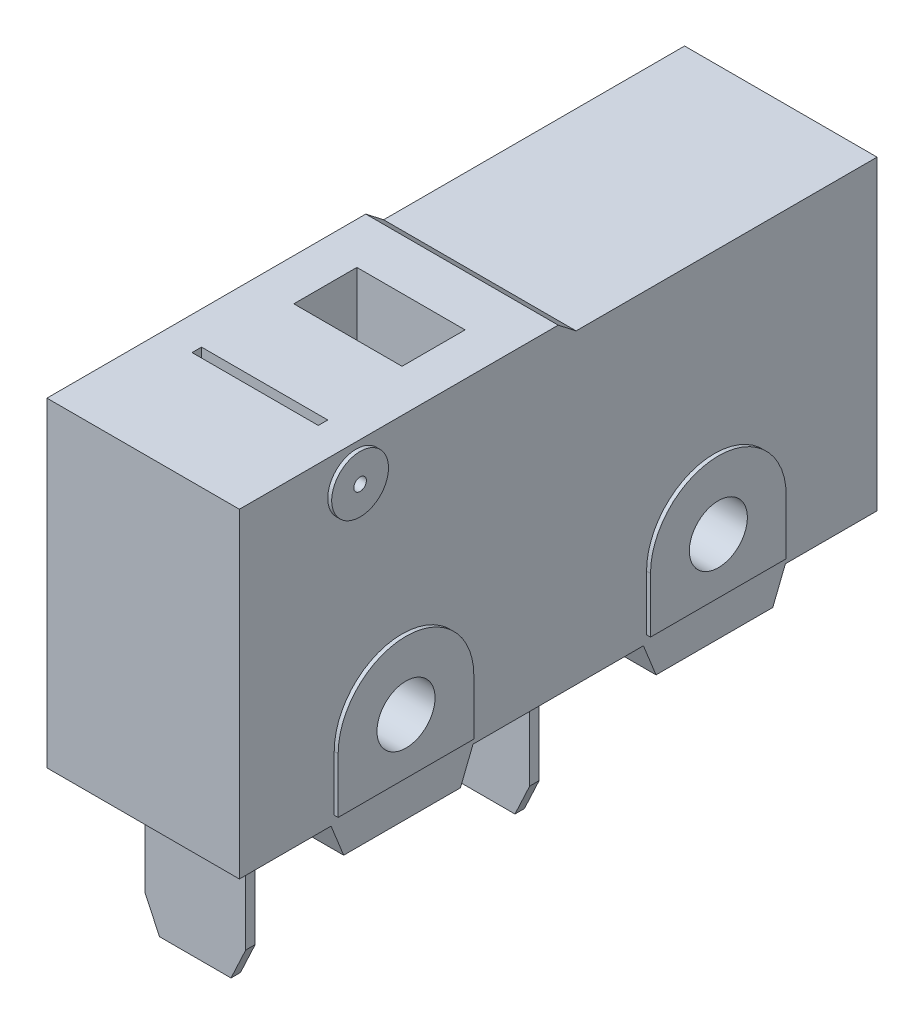
SolidWorks part; units mm, degrees
ref_plane "Front Plane" through (0, 0, 0) normal (0, 0, 1) x (1, 0, 0)
ref_plane "Top Plane" through (0, 0, 0) normal (0, 1, 0) x (1, 0, 0)
ref_plane "Right Plane" through (0, 0, 0) normal (1, 0, 0) x (0, 0, -1)
sketch "Sketch1" plane through (0, 0, 0) normal (1, 0, 0) x (0, 0, -1)
  line L1 (-10.105, 4.855) -> (10.105, 4.855)
  line L2 (-10.105, 4.855) -> (-10.105, -4.855)
  line L3 (-10.105, -4.855) -> (10.105, -4.855)
  line L4 (10.105, 4.855) -> (10.105, -4.855)
  line L5 (-10.105, 4.855) -> (10.105, -4.855) construction
  line L6 (-10.105, -4.855) -> (10.105, 4.855) construction
  point P0 (0, 0)
  point P6 (-10.105, 0)
  dimension "D1" = 20.21
  dimension "D2" = 9.71
extrude "Boss-Extrude1" add sketch "Sketch1" along normal mid plane 6.1
sketch "Sketch4" plane through (0, 0, 0) normal (1, 0, 0) x (0, 0, -1)
  line L0 (-7.2, -4.855) -> (-6.8, -5.855)
  line L1 (-7.2, -2.7338) -> (-7.2, -5.855) construction
  line L2 (-10.105, -4.855) -> (10.105, -4.855) construction
  line L3 (-7.2, -5.855) -> (-2.7, -5.855) construction
  line L4 (-6.8, -5.855) -> (-3.1, -5.855)
  line L5 (-3.1, -5.855) -> (-2.7, -4.855)
  line L6 (-2.7, -5.855) -> (-2.7, -2.7338) construction
  line L7 (-2.7, -4.855) -> (-7.2, -4.855)
  line L8 (-4.95, 0.2162) -> (-4.95, -6.3046) construction
  line L9 (0, 6.1609) -> (0, -8.528) construction
  line L10 (2.7, -4.855) -> (7.2, -4.855)
  line L11 (3.1, -5.855) -> (2.7, -4.855)
  line L12 (6.8, -5.855) -> (3.1, -5.855)
  line L13 (7.2, -4.855) -> (6.8, -5.855)
  line L14 (-10.105, 4.855) -> (-10.105, 5.295)
  line L15 (-10.105, 5.295) -> (0, 5.295)
  line L16 (0, 5.295) -> (0.5663, 4.855)
  line L17 (10.105, 4.855) -> (-10.105, 4.855) construction
  line L18 (-10.105, 4.855) -> (0.5663, 4.855)
  point P8 (-4.95, -5.855)
  dimension "D1" = 3.7
  dimension "D2" = 10.15
sketch "Mounting Holes" plane through (0, 0, 0) normal (1, 0, 0) x (0, 0, -1)
  line L0 (-10.105, -4.855) -> (10.105, -4.855) construction
  line L1 (-4.95, -2.855) -> (4.95, -2.855) construction
  circle A0 centre (-4.95, -2.855) radius 0.92
  circle A1 centre (4.95, -2.855) radius 0.92
  point P7 (0, -2.855)
  dimension "D1" = 1.84
  dimension "D2" = 2
  dimension "D3" = 9.9
sketch "Sketch3" plane through (0, 0, 0) normal (1, 0, 0) x (0, 0, -1)
  line L4 (-6.8691, -0.455) -> (-3.0762, -0.455) construction
  line L6 (-4.95, 0.2162) -> (-4.95, -6.3046) construction
  line L8 (-7.1, -2.855) -> (-7.1, -4.605)
  line L9 (-7.1, -4.605) -> (-2.8, -4.605)
  line L10 (-2.8, -4.605) -> (-2.8, -2.855)
  line L11 (-10.105, -4.855) -> (10.105, -4.855) construction
  line L12 (0, 1.4439) -> (0, -5.6534) construction
  line L13 (4.95, 0.2162) -> (4.95, -6.3046) construction
  line L14 (6.8691, -0.455) -> (3.0762, -0.455) construction
  line L15 (2.8, -4.605) -> (2.8, -2.855)
  line L16 (7.1, -4.605) -> (2.8, -4.605)
  line L17 (7.1, -2.855) -> (7.1, -4.605)
  arc A0 (-2.8, -2.855) -> (-7.1, -2.855) centre (-4.95, -2.855) ccw
  arc A1 (2.8, -2.855) -> (7.1, -2.855) centre (4.95, -2.855) cw
  dimension "D1" = 4.3
  dimension "D2" = 0.25
extrude "Boss-Extrude2" add sketch "Sketch4" along normal mid plane 6.1
extrude "Boss-Extrude3" add sketch "Sketch3" along normal mid plane 6.35
extrude "Cut-Extrude1" cut sketch "Mounting Holes" against normal through all both and the other way through all
sketch "Sketch5" plane through (0, 0, 0) normal (1, 0, 0) x (0, 0, -1)
  line L0 (-10.105, 5.295) -> (-10.105, -4.855) construction
  line L1 (0, 5.295) -> (-10.105, 5.295) construction
  circle A0 centre (-6.405, 4.195) radius 0.9
  dimension "D1" = 1.8
  dimension "D2" = 3.7
  dimension "D3" = 1.1
extrude "Boss-Extrude4" add sketch "Sketch5" along normal mid plane 6.35
sketch "Sketch6" plane through (0, 0, 0) normal (1, 0, 0) x (0, 0, -1)
  circle A0 centre (-6.405, 4.195) radius 0.2
  dimension "D1" = 0.4
extrude "Cut-Extrude2" cut sketch "Sketch6" against normal through all both and the other way through all
sketch "Sketch7" plane through (0, 5.295, 0) normal (0, 1, 0) x (1, 0, 0)
  line L0 (-3.175, -6.405) -> (3.175, -6.405) construction
  line L1 (-3.175, -5.505) -> (-3.175, -7.305) construction
  line L2 (3.175, -7.305) -> (3.175, -5.505) construction
  line L5 (-2, -6.255) -> (2, -6.255)
  line L6 (-2, -6.255) -> (-2, -6.555)
  line L7 (-2, -6.555) -> (2, -6.555)
  line L8 (2, -6.255) -> (2, -6.555)
  line L9 (-2, -6.255) -> (2, -6.555) construction
  line L10 (-2, -6.555) -> (2, -6.255) construction
  point P6 (0, -6.405)
  dimension "D1" = 4
  dimension "D2" = 0.3
extrude "Cut-Extrude3" cut sketch "Sketch7" against normal blind 5
sketch "Sketch8" plane through (0, 5.295, 0) normal (0, 1, 0) x (1, 0, 0)
  line L0 (3.05, -10.105) -> (-3.05, -10.105) construction
  line L1 (-1.7265, -3.605) -> (1.7035, -3.605)
  line L2 (-1.7265, -3.605) -> (-1.7265, -1.605)
  line L3 (-1.7265, -1.605) -> (1.7035, -1.605)
  line L4 (1.7035, -3.605) -> (1.7035, -1.605)
  line L5 (-1.7265, -3.605) -> (1.7035, -1.605) construction
  line L6 (-1.7265, -1.605) -> (1.7035, -3.605) construction
  point P0 (-0.0115, -2.605)
  dimension "D1" = 2
  dimension "D2" = 3.43
  dimension "D3" = 7.5
extrude "Cut-Extrude4" cut sketch "Sketch8" against normal blind 4
sketch "Sketch9" plane through (0, -4.855, 0) normal (0, -1, 0) x (1, 0, 0)
  line L0 (3.05, 10.105) -> (-3.05, 10.105) construction
  line L1 (1.6, 8.455) -> (-1.6, 8.455)
  line L2 (1.6, 8.455) -> (1.6, 8.155)
  line L3 (1.6, 8.155) -> (-1.6, 8.155)
  line L4 (-1.6, 8.455) -> (-1.6, 8.155)
  line L5 (1.6, 8.455) -> (-1.6, 8.155) construction
  line L6 (1.6, 8.155) -> (-1.6, 8.455) construction
  line L7 (1.6, -0.545) -> (-1.6, -0.545)
  line L8 (1.6, -0.545) -> (1.6, -0.845)
  line L9 (1.6, -0.845) -> (-1.6, -0.845)
  line L10 (-1.6, -0.545) -> (-1.6, -0.845)
  line L11 (1.6, -0.545) -> (-1.6, -0.845) construction
  line L12 (1.6, -0.845) -> (-1.6, -0.545) construction
  point P0 (0, 8.305)
  point P8 (0, -0.695)
  dimension "D1" = 1.8
  dimension "D2" = 0.3
  dimension "D3" = 3.2
  dimension "D4" = 2
extrude "Boss-Extrude5" add sketch "Sketch9" along normal blind 4.5 separate body
chamfer "Chamfer1" distance 1 angle 25 2 edges at (1.6, -9.355, -0.695) (-1.6, -9.355, -0.695)
chamfer "Chamfer2" distance 1 angle 25 2 edges at (-1.6, -9.355, 8.305) (1.6, -9.355, 8.305)
